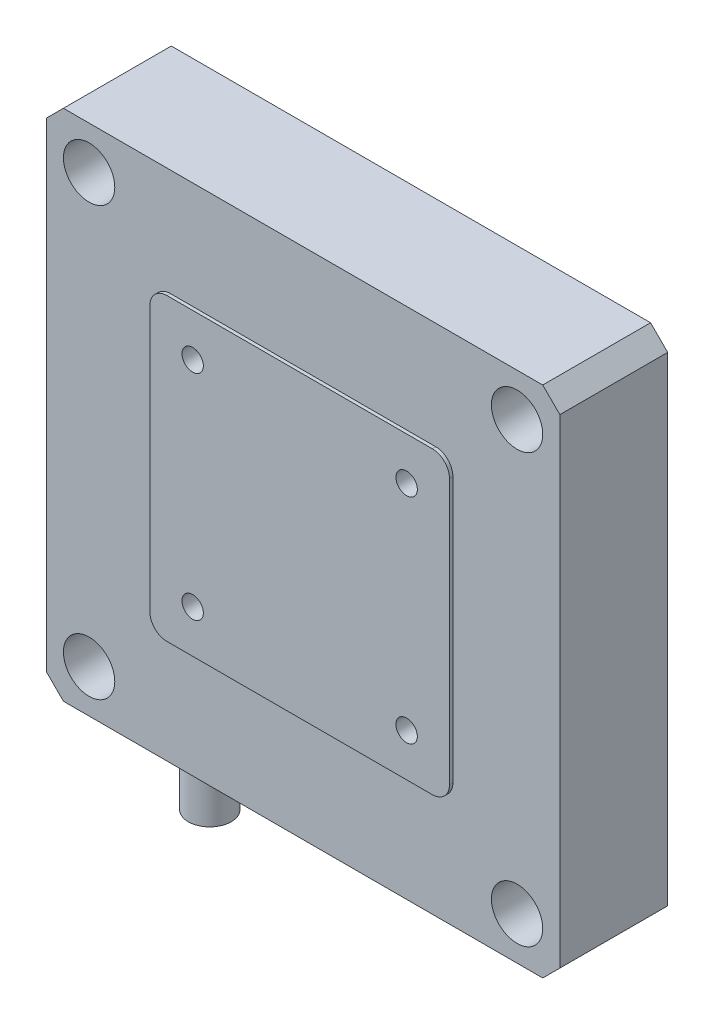
SolidWorks part; units mm, degrees
ref_plane "前视基准面" through (0, 0, 0) normal (0, 0, 1) x (1, 0, 0)
ref_plane "上视基准面" through (0, 0, 0) normal (0, 1, 0) x (1, 0, 0)
ref_plane "右视基准面" through (0, 0, 0) normal (1, 0, 0) x (0, 0, -1)
sketch "草图1" plane through (0, 0, 0) normal (0, 0, 1) x (1, 0, 0)
  line L1 (-30, 30) -> (30, 30)
  line L2 (-30, 30) -> (-30, -30)
  line L3 (-30, -30) -> (30, -30)
  line L4 (30, 30) -> (30, -30)
  line L5 (-30, 30) -> (30, -30) construction
  line L6 (-30, -30) -> (30, 30) construction
  point P0 (0, 0)
  dimension "D1" = 60
extrude "凸台-拉伸1" add sketch "草图1" along normal blind 12.6
chamfer "倒角1" distance 2 angle 45 4 edges at (-30, -30, 6.3) (30, -30, 6.3) (30, 30, 6.3) (-30, 30, 6.3)
sketch "草图2" plane through (0, 0, 12.6) normal (0, 0, 1) x (1, 0, 0)
  line L1 (-17.5, 17.5) -> (17.5, 17.5)
  line L2 (-17.5, 17.5) -> (-17.5, -17.5)
  line L3 (-17.5, -17.5) -> (17.5, -17.5)
  line L4 (17.5, 17.5) -> (17.5, -17.5)
  line L5 (-17.5, 17.5) -> (17.5, -17.5) construction
  line L6 (-17.5, -17.5) -> (17.5, 17.5) construction
  point P0 (0, 0)
  dimension "D1" = 35
extrude "凸台-拉伸2" add sketch "草图2" along normal blind 0.4
fillet "圆角1" radius 2 4 edges at (17.5, -17.5, 12.8) (-17.5, -17.5, 12.8) (17.5, 17.5, 12.8) (-17.5, 17.5, 12.8)
sketch "草图3" plane through (0, 0, 12.6) normal (0, 0, 1) x (1, 0, 0)
  line L1 (-25, 25) -> (25, 25) construction
  line L2 (-25, 25) -> (-25, -25) construction
  line L3 (-25, -25) -> (25, -25) construction
  line L4 (25, 25) -> (25, -25) construction
  line L5 (-25, 25) -> (25, -25) construction
  line L6 (-25, -25) -> (25, 25) construction
  point P0 (0, 0)
  dimension "D1" = 50
sketch "草图4" plane through (0, 0, 13) normal (0, 0, 1) x (1, 0, 0)
  line L0 (-25, -25) -> (25, 25) construction
  line L1 (-12.5, -12.5) -> (12.5, -12.5) construction
  line L2 (-12.5, -12.5) -> (-12.5, 12.5) construction
  line L3 (-12.5, 12.5) -> (12.5, 12.5) construction
  line L4 (12.5, -12.5) -> (12.5, 12.5) construction
  line L5 (-12.5, -12.5) -> (12.5, 12.5) construction
  line L6 (-12.5, 12.5) -> (12.5, -12.5) construction
  point P0 (0, 0)
  dimension "D1" = 25
hole_wizard "孔1" positions "3D草图1" profile "草图5" legacy end condition through all
sketch3d "3D草图1"
  point P0 (-25, 25, 12.6)
  point P3 (25, 25, 12.6)
  point P6 (-25, -25, 12.6)
  point P9 (25, -25, 12.6)
sketch "草图5" plane through (-25, 25, 12.6) normal (1, 0, 0) x (0, -1, 0)
  line L0 (0, 0) -> (0, 12.6)
  line L1 (0, 12.6) -> (1.7, 12.6)
  line L2 (1.7, 12.6) -> (1.7, 5)
  line L3 (1.7, 5) -> (3, 5)
  line L4 (3, 5) -> (3, 0)
  line L5 (3, 0) -> (0, 0)
  line L6 (0, 110) -> (0, -10) construction
  dimension "直径" = 3.4
  dimension "深度" = 12.6
  dimension "柱坑直径" = 6
  dimension "柱坑深度" = 5
hole_wizard "M3 螺纹孔1" positions "3D草图2" profile "草图6" tap size "M3" standard "ISO"
sketch3d "3D草图2"
  point P0 (-12.5, 12.5, 13)
  point P3 (12.5, 12.5, 13)
  point P6 (12.5, -12.5, 13)
  point P9 (-12.5, -12.5, 13)
sketch "草图6" plane through (-12.5, 12.5, 13) normal (1, 0, 0) x (0, -1, 0)
  line L0 (0, 0) -> (0, 4.2511)
  line L1 (0, 4.2511) -> (1.25, 3.5)
  line L2 (1.25, 3.5) -> (1.25, 0)
  line L5 (1.25, 0) -> (0, 0)
  line L10 (0, 4.2511) -> (-1.25, 3.5) construction
  line L11 (0, -6.35) -> (0, 107.95) construction
  dimension "螺纹孔钻头直径" = 2.5
  dimension "螺纹孔钻头深度" = 3.5
  dimension "导头角度" = 118
cosmetic thread "孔螺蚊线1" parameters "D1"=3.5, "D2"=3
cosmetic thread "孔螺蚊线2" parameters "D1"=3.5, "D2"=3
cosmetic thread "孔螺蚊线3" parameters "D1"=3.5, "D2"=3
cosmetic thread "孔螺蚊线4" parameters "D1"=3.5, "D2"=3
sketch "草图7" plane through (0, -30, 0) normal (0, -1, 0) x (1, 0, 0)
  line L0 (-28, 0) -> (28, 0) construction
  line L1 (-30, 0) -> (-30, 12.6) construction
  circle A0 centre (-18.5, 5) radius 2.5
  dimension "D1" = 5
  dimension "D2" = 11.5
  dimension "D3" = 5
extrude "凸台-拉伸3" add sketch "草图7" along normal blind 10
